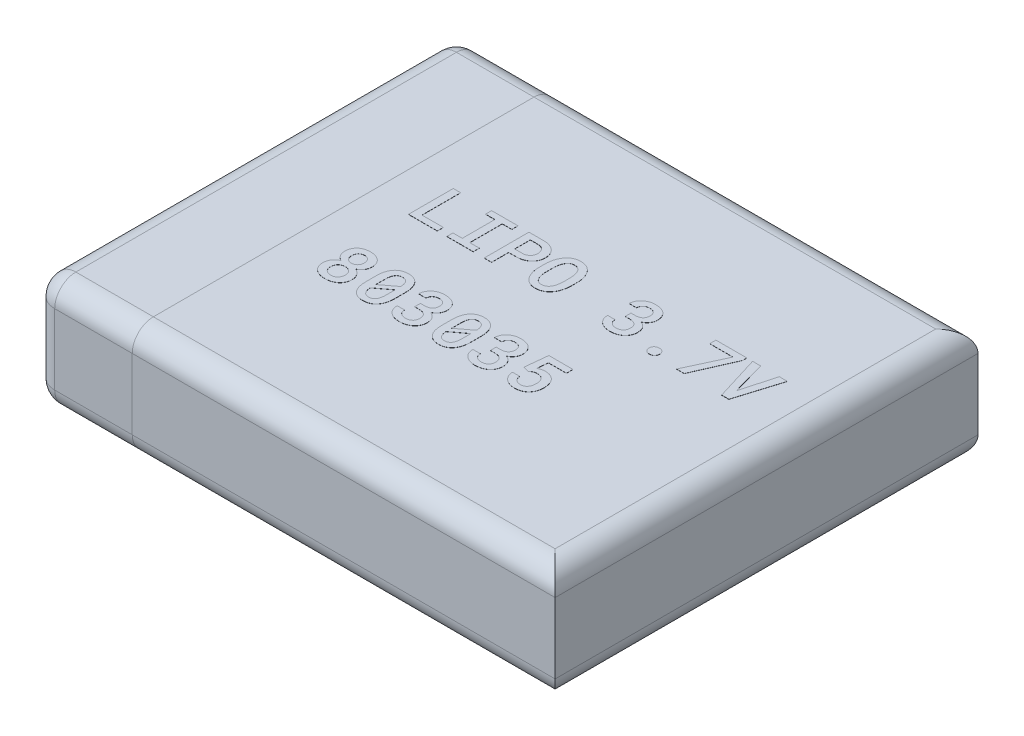
SolidWorks part; units mm, degrees
ref_plane "Front Plane" through (0, 0, 0) normal (0, 0, 1) x (1, 0, 0)
ref_plane "Top Plane" through (0, 0, 0) normal (0, 1, 0) x (1, 0, 0)
ref_plane "Right Plane" through (0, 0, 0) normal (1, 0, 0) x (0, 0, -1)
sketch "Sketch1" plane through (0, 0, 0) normal (0, 1, 0) x (1, 0, 0)
  line L1 (-19.6052, -20.8717) -> (10.3948, -20.8717)
  line L2 (-19.6052, -20.8717) -> (-19.6052, 9.1283)
  line L3 (-19.6052, 9.1283) -> (10.3948, 9.1283)
  line L4 (10.3948, -20.8717) -> (10.3948, 9.1283)
  dimension "D1" = 30
  dimension "D2" = 30
extrude "Boss-Extrude1" add sketch "Sketch1" along normal blind 8
sketch "Sketch2" plane through (-19.6052, 0, 0) normal (-1, 0, 0) x (0, 0, 1)
  line L1 (-9.1283, 8) -> (20.8717, 8)
  line L2 (-9.1283, 8) -> (-9.1283, 0)
  line L3 (-9.1283, 0) -> (20.8717, 0)
  line L4 (20.8717, 8) -> (20.8717, 0)
extrude "Boss-Extrude3" add sketch "Sketch2" along normal blind 7 separate body
fillet "Fillet1" radius 1.5 6 edges at (10.3948, 8, 5.8717) (10.3948, 0, 5.8717) (-4.6052, 0, 20.8717) (-4.6052, 0, -9.1283) (-4.6052, 8, -9.1283) (-4.6052, 8, 20.8717)
fillet "Fillet2" radius 1.5 8 edges at (-26.6052, 4, 20.8717) (-23.1052, 8, 20.8717) (-23.1052, 0, 20.8717) (-23.1052, 0, -9.1283) (-26.6052, 0, 5.8717) (-26.6052, 8, 5.8717) (-26.6052, 4, -9.1283) (-23.1052, 8, -9.1283)
sketch "Sketch3" plane through (0, 8, 0) normal (0, 1, 0) x (1, 0, 0)
  text T0 "<b>LIPO 3.7V</b>\r\n<b>803035</b>" font "Roboto Mono Medium" height 3.175
extrude "Boss-Extrude5" add sketch "Sketch3" along normal blind 0.01 separate body
